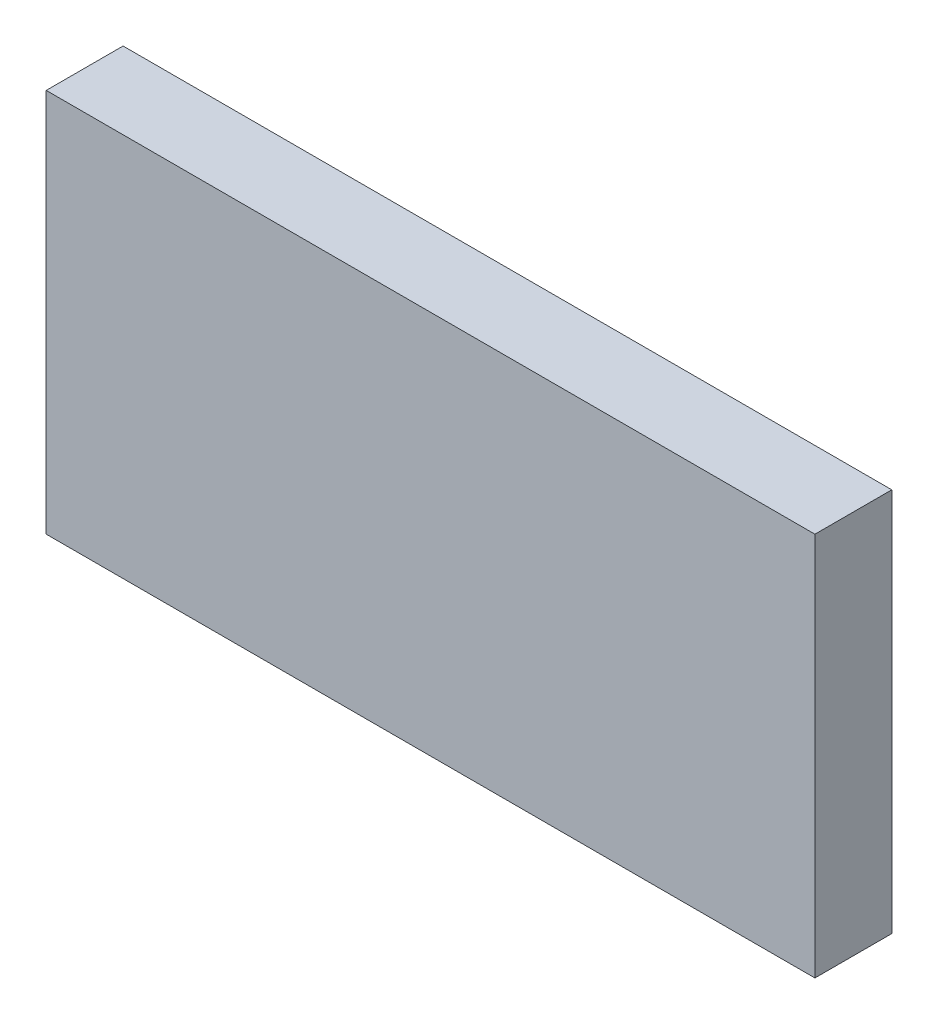
SolidWorks part; units mm, degrees
ref_plane "Ebene vorne" through (0, 0, 0) normal (0, 0, 1) x (1, 0, 0)
ref_plane "Ebene oben" through (0, 0, 0) normal (0, 1, 0) x (1, 0, 0)
ref_plane "Ebene rechts" through (0, 0, 0) normal (1, 0, 0) x (0, 0, -1)
sketch "Skizze1" plane through (0, 0, 0) normal (0, 0, 1) x (1, 0, 0)
  line L1 (0, 0) -> (100, 0)
  line L2 (0, 0) -> (0, -50)
  line L3 (0, -50) -> (100, -50)
  line L4 (100, 0) -> (100, -50)
  dimension "D1" = 100
  dimension "D2" = 50
extrude "Aufsatz-Linear austragen1" add sketch "Skizze1" along normal blind 10
